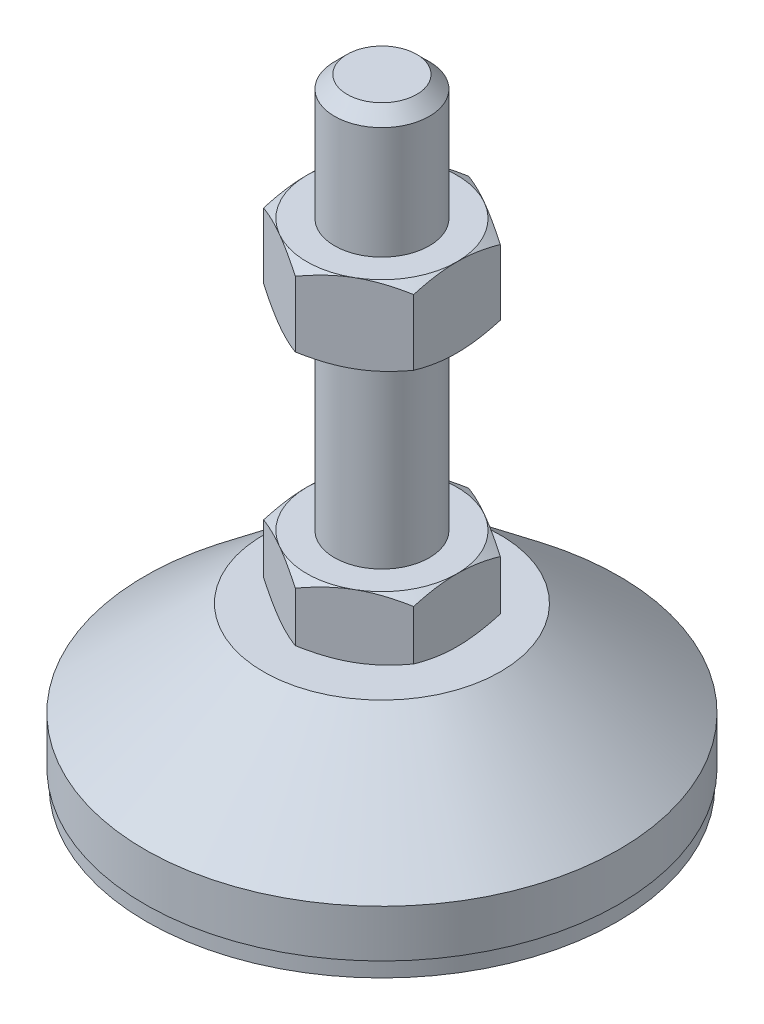
SolidWorks part; units mm, degrees
ref_plane "Спереди" through (0, 0, 0) normal (0, 0, 1) x (1, 0, 0)
ref_plane "Сверху" through (0, 0, 0) normal (0, 1, 0) x (1, 0, 0)
ref_plane "Справа" through (0, 0, 0) normal (1, 0, 0) x (0, 0, -1)
sketch "Эскиз1" plane through (0, 0, 0) normal (0, 0, 1) x (1, 0, 0)
  line L0 (0, 0) -> (-29.8, 0)
  line L1 (-29.8, 0) -> (-29.8, 2)
  line L2 (-29.8, 2) -> (-30, 2)
  line L3 (-30, 2) -> (-30, 8)
  line L4 (-30, 8) -> (-15, 20)
  line L5 (-15, 20) -> (-6, 20)
  line L12 (-6, 28) -> (-6, 76.4)
  line L13 (-6, 76.4) -> (-4.4, 78)
  line L14 (-4.4, 78) -> (0, 78)
  line L15 (0, 78) -> (0, 0) construction
  line L16 (-6, 20) -> (0, 20) construction
  line L17 (0, 0) -> (0, 78)
  line L18 (0, 0) -> (0, -7.9595) construction
  line L19 (-6, 28) -> (-6, 20)
  point P8 (-6, 52.2)
  point P23 (-10.5, 20)
  dimension "D1" = 12
  dimension "D2" = 20
  dimension "D3" = 8
  dimension "D4" = 60
  dimension "D5" = 6
  dimension "D6" = 1.6
  dimension "D7" = 45
  dimension "D8" = 30
  dimension "D9" = 2
  dimension "D10" = 50
  dimension "D11" = 6
  dimension "D12" = 0.2
revolve "Повернуть1" add sketch "Эскиз1" angle 360 about L17
sketch "Эскиз2" plane through (0, 20, 0) normal (0, 1, 0) x (1, 0, 0)
  line L1 (0, 10.9697) -> (-9.5, 5.4848)
  line L2 (-9.5, 5.4848) -> (-9.5, -5.4848)
  line L3 (-9.5, -5.4848) -> (0, -10.9697)
  line L4 (0, -10.9697) -> (9.5, -5.4848)
  line L5 (9.5, -5.4848) -> (9.5, 5.4848)
  line L6 (9.5, 5.4848) -> (0, 10.9697)
  circle A0 centre (0, 0) radius 9.5 construction
  dimension "D1" = 19
extrude "Бобышка-Вытянуть1" add sketch "Эскиз2" along normal up to vertex (8 mm away) up to point (-6, 28, 0)
ref_plane "Плоскость1" through (0, 52.2, 0) normal (0, 1, 0) x (1, 0, 0)
sketch "Эскиз3" plane through (0, 52.2, 0) normal (0, 1, 0) x (1, 0, 0)
  line L6 (9.5, 5.4848) -> (0, 10.9697)
  line L7 (0, 10.9697) -> (-9.5, 5.4848)
  line L8 (-9.5, 5.4848) -> (-9.5, -5.4848)
  line L9 (-9.5, -5.4848) -> (0, -10.9697)
  line L10 (0, -10.9697) -> (9.5, -5.4848)
  line L11 (9.5, -5.4848) -> (9.5, 5.4848)
  line L12 (9.5, 5.4848) -> (0, 10.9697)
  line L13 (0, 10.9697) -> (-9.5, 5.4848)
  line L14 (-9.5, 5.4848) -> (-9.5, -5.4848)
  line L15 (-9.5, -5.4848) -> (0, -10.9697)
  line L16 (0, -10.9697) -> (9.5, -5.4848)
  line L17 (9.5, -5.4848) -> (9.5, 5.4848)
  dimension "D1" = 0
extrude "Бобышка-Вытянуть2" add sketch "Эскиз3" along normal blind 10
sketch "Эскиз4" plane through (0, 0, 0) normal (0, 0, 1) x (1, 0, 0)
  line L0 (-9.5, 62.2) -> (-18.1603, 57.2)
  line L1 (-18.1603, 57.2) -> (-18.1603, 62.2)
  line L2 (-18.1603, 62.2) -> (-9.5, 62.2)
  line L3 (-18.1603, 57.2) -> (-9.5, 52.2)
  line L4 (50, 52.2) -> (-50, 52.2) construction
  line L5 (-9.5, 52.2) -> (-18.1603, 52.2)
  line L6 (-18.1603, 52.2) -> (-18.1603, 57.2)
  line L7 (-9.5, 62.2) -> (-9.5, 52.2) construction
  line L8 (-9.5, 28) -> (-16.4282, 28)
  line L9 (-16.4282, 28) -> (-16.4282, 24)
  line L10 (-16.4282, 24) -> (-9.5, 28)
  line L11 (-9.5, 20) -> (-16.4282, 24)
  line L12 (-16.4282, 24) -> (-16.4282, 20)
  line L13 (-16.4282, 20) -> (-9.5, 20)
  line L14 (0, 78) -> (0, 96.3793) construction
  dimension "D1" = 30
  dimension "D2" = 30
revolve "Вырез-Повернуть2" cut sketch "Эскиз4" angle 360 about L14
